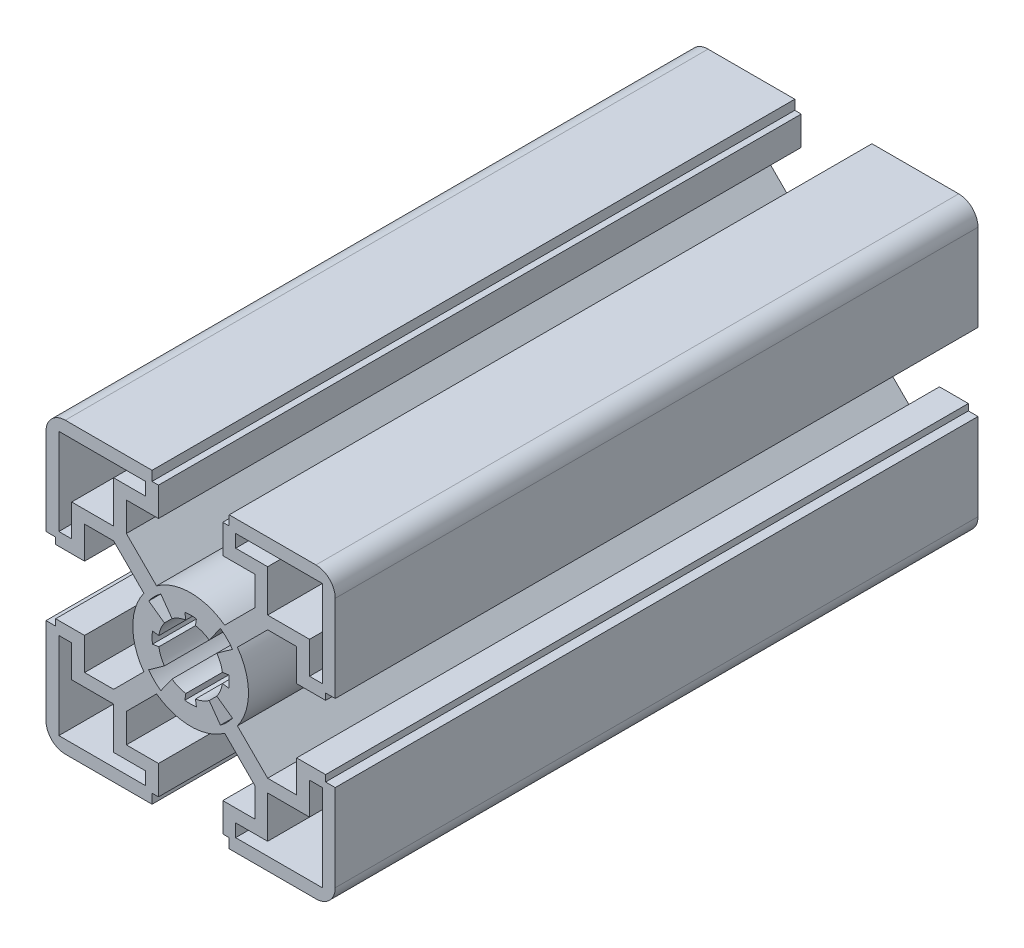
SolidWorks part; units mm, degrees
ref_plane "Ön Düzlem" through (0, 0, 0) normal (0, 0, 1) x (1, 0, 0)
ref_plane "Üst Düzlem" through (0, 0, 0) normal (0, 1, 0) x (1, 0, 0)
ref_plane "Sağ Düzlem" through (0, 0, 0) normal (1, 0, 0) x (0, 0, -1)
ref_plane "Düzlem1" through (0, 0, 100) normal (0, 0, 1) x (1, 0, 0)
sketch "Çizim1" plane through (0, 0, 100) normal (0, 0, 1) x (1, 0, 0)
  line L0 (5, -21) -> (6, -21)
  line L1 (6, -21) -> (6, -22.5)
  line L2 (6, -22.5) -> (19.5, -22.5)
  line L3 (22.5, -19.5) -> (22.5, -6)
  line L4 (22.5, -6) -> (21, -6)
  line L5 (21, -6) -> (21, -5)
  line L6 (21, -5) -> (16.5, -5)
  line L7 (16.5, -5) -> (16.5, -10)
  line L8 (16.5, -10) -> (11.9799, -10)
  line L9 (11.9799, -10) -> (7.2764, -5.2965)
  line L10 (7.2764, 5.2965) -> (11.9799, 10)
  line L11 (11.9799, 10) -> (16.5, 10)
  line L12 (16.5, 10) -> (16.5, 5)
  line L13 (16.5, 5) -> (21, 5)
  line L14 (21, 5) -> (21, 6)
  line L15 (21, 6) -> (22.5, 6)
  line L16 (22.5, 6) -> (22.5, 19.5)
  line L17 (19.5, 22.5) -> (6, 22.5)
  line L18 (6, 22.5) -> (6, 21)
  line L19 (6, 21) -> (5, 21)
  line L20 (5, 21) -> (5, 16.5)
  line L21 (5, 16.5) -> (10, 16.5)
  line L22 (10, 16.5) -> (10, 11.9799)
  line L23 (10, 11.9799) -> (5.2965, 7.2764)
  line L24 (-5.2965, 7.2764) -> (-10, 11.9799)
  line L25 (-10, 11.9799) -> (-10, 16.5)
  line L26 (-10, 16.5) -> (-5, 16.5)
  line L27 (-5, 16.5) -> (-5, 21)
  line L28 (-5, 21) -> (-6, 21)
  line L29 (-6, 21) -> (-6, 22.5)
  line L30 (-6, 22.5) -> (-19.5, 22.5)
  line L31 (-22.5, 19.5) -> (-22.5, 6)
  line L32 (-22.5, 6) -> (-21, 6)
  line L33 (-21, 6) -> (-21, 5)
  line L34 (-21, 5) -> (-16.5, 5)
  line L35 (-16.5, 5) -> (-16.5, 10)
  line L36 (-16.5, 10) -> (-11.9799, 10)
  line L37 (-11.9799, 10) -> (-7.2764, 5.2965)
  line L38 (-7.2764, -5.2965) -> (-11.9799, -10)
  line L39 (-11.9799, -10) -> (-16.5, -10)
  line L40 (-16.5, -10) -> (-16.5, -5)
  line L41 (-16.5, -5) -> (-21, -5)
  line L42 (-21, -5) -> (-21, -6)
  line L43 (-21, -6) -> (-22.5, -6)
  line L44 (-22.5, -6) -> (-22.5, -19.5)
  line L45 (-19.5, -22.5) -> (-6, -22.5)
  line L46 (-6, -22.5) -> (-6, -21)
  line L47 (-6, -21) -> (-5, -21)
  line L48 (-5, -21) -> (-5, -16.5)
  line L49 (-5, -16.5) -> (-10, -16.5)
  line L50 (-10, -16.5) -> (-10, -11.9799)
  line L51 (-10, -11.9799) -> (-5.2965, -7.2764)
  line L52 (5.2965, -7.2764) -> (10, -11.9799)
  line L53 (10, -11.9799) -> (10, -16.5)
  line L54 (10, -16.5) -> (5, -16.5)
  line L55 (5, -16.5) -> (5, -21)
  line L56 (-11.98, 18.5001) -> (-11.98, 11.98)
  line L57 (-11.98, 11.98) -> (-18.5001, 11.98)
  line L58 (-18.5001, 11.98) -> (-18.5001, 7.0001)
  line L59 (-18.5001, 7.0001) -> (-20.5001, 7.0001)
  line L60 (-20.5001, 7.0001) -> (-20.5001, 20.5001)
  line L61 (-20.5001, 20.5001) -> (-7.0001, 20.5001)
  line L62 (-7.0001, 20.5001) -> (-7.0001, 18.5001)
  line L63 (-7.0001, 18.5001) -> (-11.98, 18.5001)
  line L64 (-18.5001, -11.98) -> (-11.98, -11.98)
  line L65 (-11.98, -11.98) -> (-11.98, -18.5001)
  line L66 (-11.98, -18.5001) -> (-7.0001, -18.5001)
  line L67 (-7.0001, -18.5001) -> (-7.0001, -20.5001)
  line L68 (-7.0001, -20.5001) -> (-20.5001, -20.5001)
  line L69 (-20.5001, -20.5001) -> (-20.5001, -7.0001)
  line L70 (-20.5001, -7.0001) -> (-18.5001, -7.0001)
  line L71 (-18.5001, -7.0001) -> (-18.5001, -11.98)
  line L72 (11.98, -18.5001) -> (11.98, -11.98)
  line L73 (11.98, -11.98) -> (18.5001, -11.98)
  line L74 (18.5001, -11.98) -> (18.5001, -7.0001)
  line L75 (18.5001, -7.0001) -> (20.5001, -7.0001)
  line L76 (20.5001, -7.0001) -> (20.5001, -20.5001)
  line L77 (20.5001, -20.5001) -> (7.0001, -20.5001)
  line L78 (7.0001, -20.5001) -> (7.0001, -18.5001)
  line L79 (7.0001, -18.5001) -> (11.98, -18.5001)
  line L80 (18.5001, 11.98) -> (11.98, 11.98)
  line L81 (11.98, 11.98) -> (11.98, 18.5001)
  line L82 (11.98, 18.5001) -> (7.0001, 18.5001)
  line L83 (7.0001, 18.5001) -> (7.0001, 20.5001)
  line L84 (7.0001, 20.5001) -> (20.5001, 20.5001)
  line L85 (20.5001, 20.5001) -> (20.5001, 7.0001)
  line L86 (20.5001, 7.0001) -> (18.5001, 7.0001)
  line L87 (18.5001, 7.0001) -> (18.5001, 11.98)
  line L88 (-6.5202, -4.6354) -> (-4.0751, -2.8971)
  line L89 (-4.9435, -0.7494) -> (-5.9322, -0.8993)
  line L90 (-5.9322, 0.8993) -> (-4.9435, 0.7494)
  line L91 (-4.0751, 2.8971) -> (-6.5202, 4.6354)
  line L92 (-4.6354, 6.5202) -> (-2.8971, 4.0751)
  line L93 (-0.7494, 4.9435) -> (-0.8993, 5.9322)
  line L94 (0.8993, 5.9322) -> (0.7494, 4.9435)
  line L95 (2.8971, 4.0751) -> (4.6354, 6.5202)
  line L96 (6.5202, 4.6354) -> (4.0751, 2.8971)
  line L97 (4.9435, 0.7494) -> (5.9322, 0.8993)
  line L98 (5.9322, -0.8993) -> (4.9435, -0.7494)
  line L99 (4.0751, -2.8971) -> (6.5202, -4.6354)
  line L100 (4.6354, -6.5202) -> (2.8971, -4.0751)
  line L101 (0.7494, -4.9435) -> (0.8993, -5.9322)
  line L102 (-0.8993, -5.9322) -> (-0.7494, -4.9435)
  line L103 (-2.8971, -4.0751) -> (-4.6354, -6.5202)
  arc A0 (19.5, -22.5) -> (22.5, -19.5) centre (19.5, -19.5) ccw
  arc A1 (7.2764, -5.2965) -> (7.2764, 5.2965) centre (0, 0) ccw
  arc A2 (22.5, 19.5) -> (19.5, 22.5) centre (19.5, 19.5) ccw
  arc A3 (5.2965, 7.2764) -> (-5.2965, 7.2764) centre (0, 0) ccw
  arc A4 (-19.5, 22.5) -> (-22.5, 19.5) centre (-19.5, 19.5) ccw
  arc A5 (-7.2764, 5.2965) -> (-7.2764, -5.2965) centre (0, 0) ccw
  arc A6 (-22.5, -19.5) -> (-19.5, -22.5) centre (-19.5, -19.5) ccw
  arc A7 (-5.2965, -7.2764) -> (5.2965, -7.2764) centre (0, 0) ccw
  arc A8 (-4.0751, -2.8971) -> (-4.9435, -0.7494) centre (0, 0) cw
  arc A9 (-5.9322, -0.8993) -> (-5.9322, 0.8993) centre (0, 0) cw
  arc A10 (-4.9435, 0.7494) -> (-4.0751, 2.8971) centre (0, 0) cw
  arc A11 (-6.5202, 4.6354) -> (-4.6354, 6.5202) centre (0, 0) cw
  arc A12 (-2.8971, 4.0751) -> (-0.7494, 4.9435) centre (0, 0) cw
  arc A13 (-0.8993, 5.9322) -> (0.8993, 5.9322) centre (0, 0) cw
  arc A14 (0.7494, 4.9435) -> (2.8971, 4.0751) centre (0, 0) cw
  arc A15 (4.6354, 6.5202) -> (6.5202, 4.6354) centre (0, 0) cw
  arc A16 (4.0751, 2.8971) -> (4.9435, 0.7494) centre (0, 0) cw
  arc A17 (5.9322, 0.8993) -> (5.9322, -0.8993) centre (0, 0) cw
  arc A18 (4.9435, -0.7494) -> (4.0751, -2.8971) centre (0, 0) cw
  arc A19 (6.5202, -4.6354) -> (4.6354, -6.5202) centre (0, 0) cw
  arc A20 (2.8971, -4.0751) -> (0.7494, -4.9435) centre (0, 0) cw
  arc A21 (0.8993, -5.9322) -> (-0.8993, -5.9322) centre (0, 0) cw
  arc A22 (-0.7494, -4.9435) -> (-2.8971, -4.0751) centre (0, 0) cw
  arc A23 (-4.6354, -6.5202) -> (-6.5202, -4.6354) centre (0, 0) cw
extrude "Yükseklik-Ekstrüzyon1" add sketch "Çizim1" against normal blind 100
